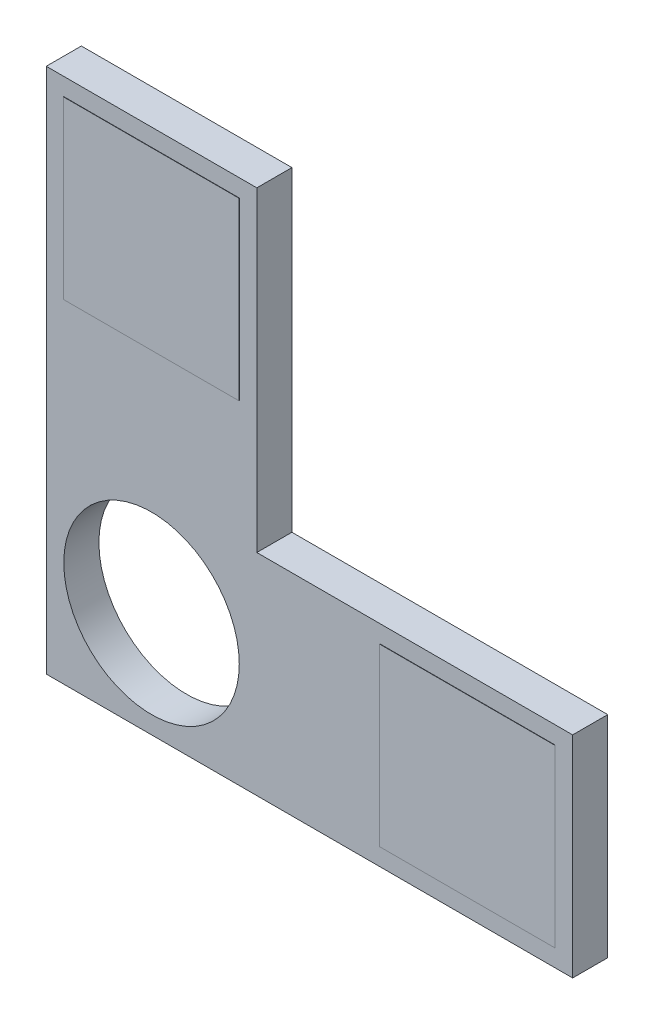
SolidWorks part; units mm, degrees
ref_plane "Front Plane" through (0, 0, 0) normal (0, 0, 1) x (1, 0, 0)
ref_plane "Top Plane" through (0, 0, 0) normal (0, 1, 0) x (1, 0, 0)
ref_plane "Right Plane" through (0, 0, 0) normal (1, 0, 0) x (0, 0, -1)
sketch "Sketch1" plane through (0, 0, 0) normal (0, 0, 1) x (1, 0, 0)
  line L0 (0, 0) -> (0, 150)
  line L1 (0, 150) -> (60, 150)
  line L2 (60, 150) -> (60, 60)
  line L3 (60, 60) -> (150, 60)
  line L4 (150, 60) -> (150, 0)
  line L5 (150, 0) -> (0, 0)
  circle A0 centre (30, 30) radius 25
  point P3 (0, 0)
  point P10 (150, 30)
  point P11 (0, 0)
  point P12 (30, 150)
  dimension "D1" = 50
  dimension "D2" = 150
  dimension "D3" = 60
extrude "Boss-Extrude1" add sketch "Sketch1" along normal blind 10
sketch "Sketch2" plane through (0, 0, 10) normal (0, 0, 1) x (1, 0, 0)
  line L0 (0, 0) -> (60, 60) construction
  line L1 (60, 150) -> (0, 150) construction
  line L2 (5, 145) -> (55, 145)
  line L3 (5, 145) -> (5, 95)
  line L4 (5, 95) -> (55, 95)
  line L5 (55, 145) -> (55, 95)
  line L6 (60, 60) -> (60, 150) construction
  line L7 (0, 150) -> (0, 0) construction
  line L8 (145, 55) -> (95, 55)
  line L9 (145, 5) -> (145, 55)
  line L10 (145, 5) -> (95, 5)
  line L11 (95, 5) -> (95, 55)
  dimension "D1" = 5
  dimension "D2" = 5
  dimension "D3" = 5
extrude "Boss-Extrude2" add sketch "Sketch2" along normal blind 0.1
equation "\"D2@Sketch2\"=\"D1@Sketch2\""
equation "\"D3@Sketch2\"=\"D1@Sketch2\""
